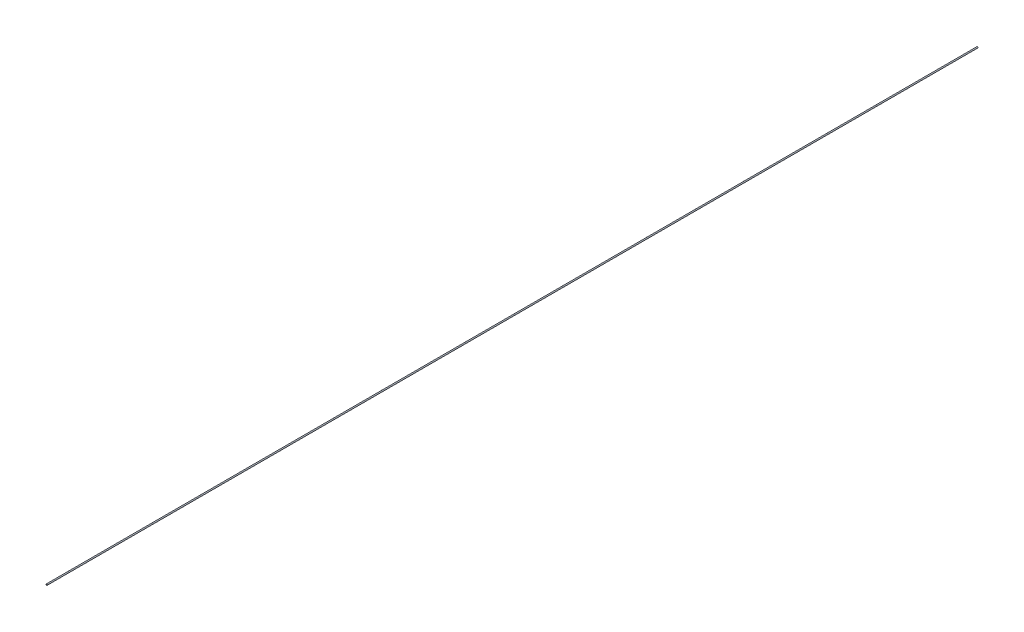
SolidWorks part; units mm, degrees
material "C (Graphite)"
ref_plane "Front Plane" through (0, 0, 0) normal (0, 0, 1) x (1, 0, 0)
ref_plane "Top Plane" through (0, 0, 0) normal (0, 1, 0) x (1, 0, 0)
ref_plane "Right Plane" through (0, 0, 0) normal (1, 0, 0) x (0, 0, -1)
sketch "Sketch1" plane through (0, 0, 0) normal (0, 0, 1) x (1, 0, 0)
  circle A0 centre (0, 0) radius 0.035
  dimension "D1" = 0.07
extrude "Boss-Extrude1" add sketch "Sketch1" along normal blind 55.9
